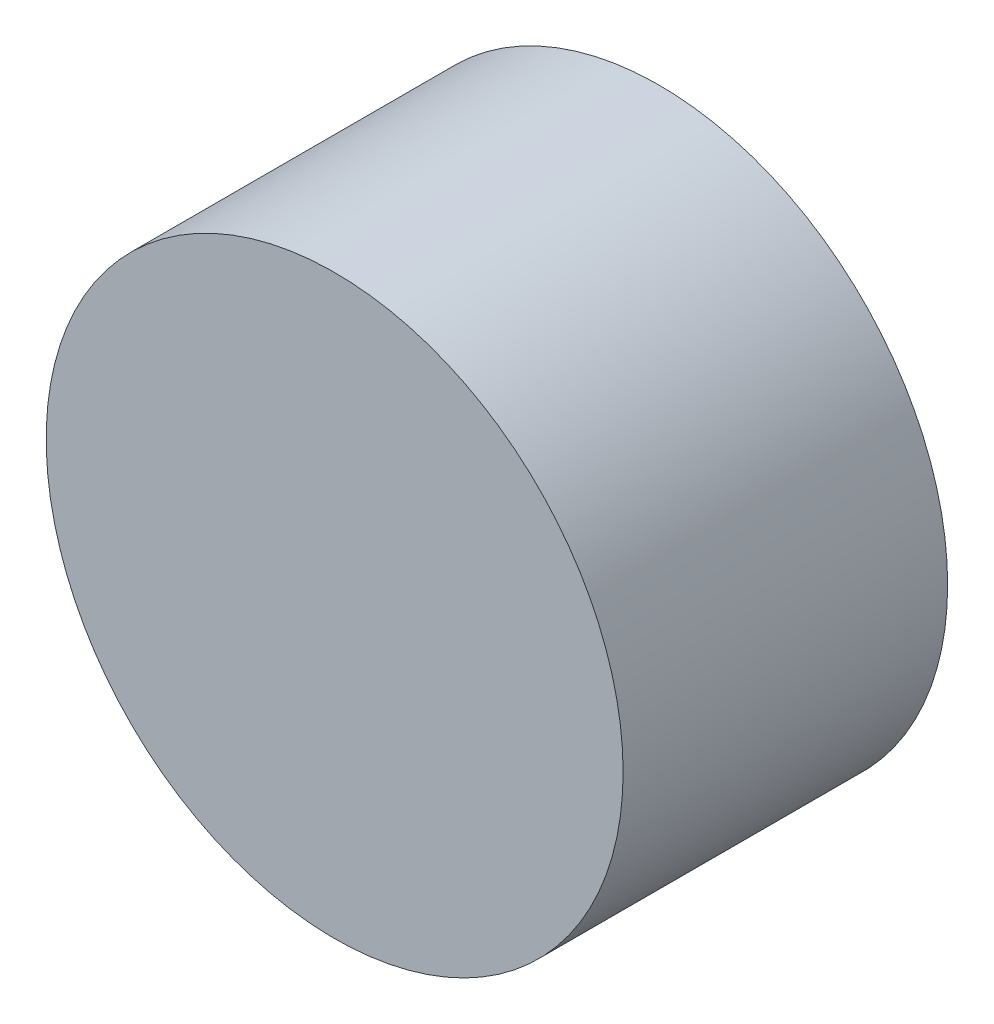
SolidWorks part; units mm, degrees
material "Tungsten"
ref_plane "Front Plane" through (0, 0, 0) normal (0, 0, 1) x (1, 0, 0)
ref_plane "Top Plane" through (0, 0, 0) normal (0, 1, 0) x (1, 0, 0)
ref_plane "Right Plane" through (0, 0, 0) normal (1, 0, 0) x (0, 0, -1)
sketch "Sketch1" plane through (0, 0, 0) normal (0, 0, 1) x (1, 0, 0)
  circle A0 centre (0, 0) radius 32
  dimension "D1" = 64
extrude "Boss-Extrude1" add sketch "Sketch1" along normal blind 36
